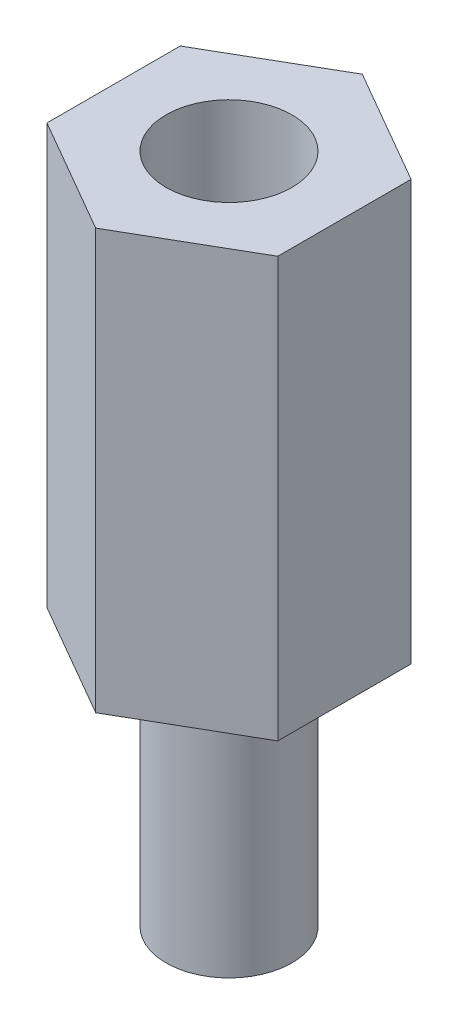
SolidWorks part; units mm, degrees
ref_plane "Alzado" through (0, 0, 0) normal (0, 0, 1) x (1, 0, 0)
ref_plane "Planta" through (0, 0, 0) normal (0, 1, 0) x (1, 0, 0)
ref_plane "Vista lateral" through (0, 0, 0) normal (1, 0, 0) x (0, 0, -1)
sketch "Croquis1" plane through (0, 0, 0) normal (0, 1, 0) x (1, 0, 0)
  line L1 (0, 3.1754) -> (-2.75, 1.5877)
  line L2 (-2.75, 1.5877) -> (-2.75, -1.5877)
  line L3 (-2.75, -1.5877) -> (0, -3.1754)
  line L4 (0, -3.1754) -> (2.75, -1.5877)
  line L5 (2.75, -1.5877) -> (2.75, 1.5877)
  line L6 (2.75, 1.5877) -> (0, 3.1754)
  circle A0 centre (0, 0) radius 2.75 construction
  dimension "D1" = 5.5
extrude "Saliente-Extruir1" add sketch "Croquis1" along normal blind 10
sketch "Croquis2" plane through (0, 0, 0) normal (0, -1, 0) x (1, 0, 0)
  circle A0 centre (0, 0) radius 1.5
  dimension "D1" = 3
extrude "Saliente-Extruir2" add sketch "Croquis2" along normal blind 6
sketch "Croquis3" plane through (0, 10, 0) normal (0, 1, 0) x (1, 0, 0)
  circle A0 centre (0, 0) radius 1.5
  dimension "D1" = 3
extrude "Cortar-Extruir1" cut sketch "Croquis3" against normal blind 6
